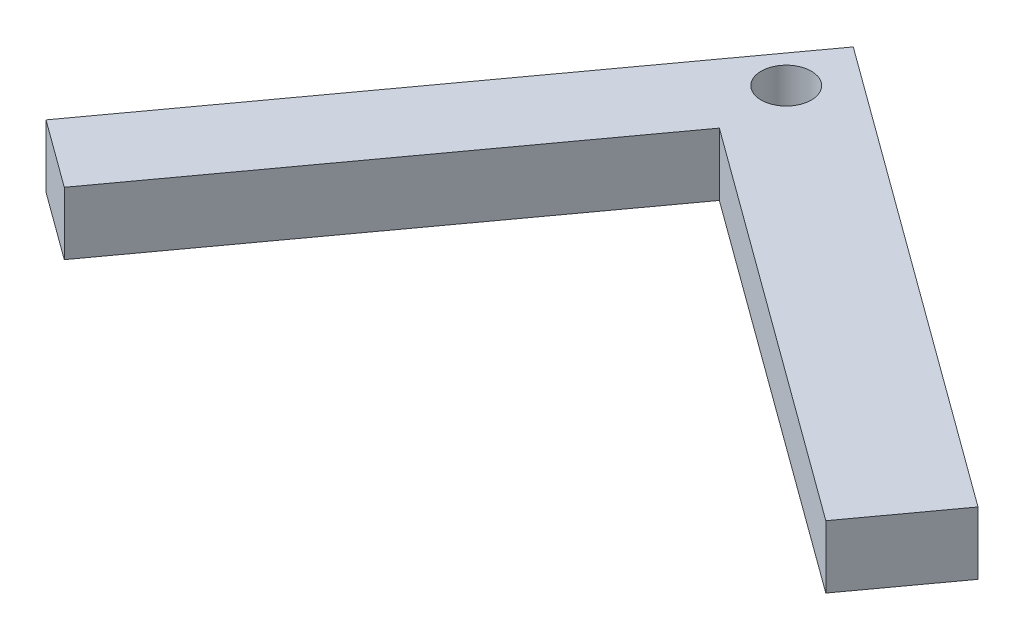
SolidWorks part; units mm, degrees
ref_plane "Front Plane" through (0, 0, 0) normal (0, 0, 1) x (1, 0, 0)
ref_plane "Top Plane" through (0, 0, 0) normal (0, 1, 0) x (1, 0, 0)
ref_plane "Right Plane" through (0, 0, 0) normal (1, 0, 0) x (0, 0, -1)
sketch "Sketch1" plane through (0, 0, 0) normal (0, 1, 0) x (1, 0, 0)
  line L7 (0, 0) -> (-16.7911, -23.024)
  line L8 (0, 0) -> (23.9023, -17.4316)
  line L15 (27.8033, -12.0826) -> (-0.2035, 8.3423)
  line L16 (-20.8955, -20.0307) -> (-0.2035, 8.3423)
  line L18 (23.9023, -17.4316) -> (27.8033, -12.0826)
  line L19 (23.9023, -17.4316) -> (25.8528, -14.7571)
  line L20 (-16.7911, -23.024) -> (-20.8955, -20.0307)
  line L21 (25.8528, -14.7571) -> (0, 4.097)
  dimension "D1" = 90
extrude "Boss-Extrude1" add sketch "Sketch1" along normal blind 3.81 contours L8 L7 L20 L16 L15 L18
sketch "Sketch2" plane through (0, 3.81, 0) normal (0, 1, 0) x (1, 0, 0)
  line L0 (-0.2035, 8.3423) -> (-0.2035, 4.2683)
  circle A0 centre (-0.2035, 4.2683) radius 1.524
  dimension "D1" = 3.048
extrude "Cut-Extrude1" cut sketch "Sketch2" against normal through all
